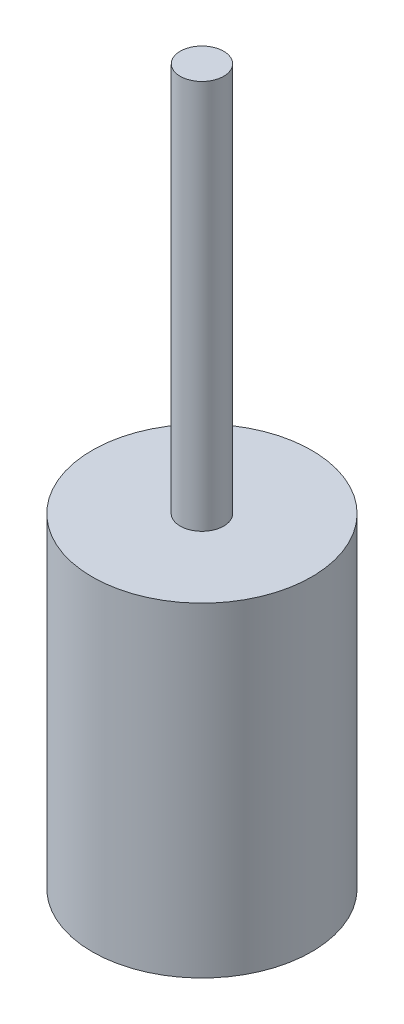
SolidWorks part; units mm, degrees
ref_plane "Front Plane" through (0, 0, 0) normal (0, 0, 1) x (1, 0, 0)
ref_plane "Top Plane" through (0, 0, 0) normal (0, 1, 0) x (1, 0, 0)
ref_plane "Right Plane" through (0, 0, 0) normal (1, 0, 0) x (0, 0, -1)
sketch "Sketch1" plane through (0, 0, 0) normal (0, 1, 0) x (1, 0, 0)
  circle A0 centre (0, 0) radius 21.463
  dimension "D1" = 42.926
extrude "Boss-Extrude1" add sketch "Sketch1" along normal blind 63.5
sketch "Sketch2" plane through (0, 63.5, 0) normal (0, 1, 0) x (1, 0, 0)
  circle A0 centre (0, 0) radius 4.25
  dimension "D1" = 8.5
extrude "Boss-Extrude2" add sketch "Sketch2" along normal blind 76.2
